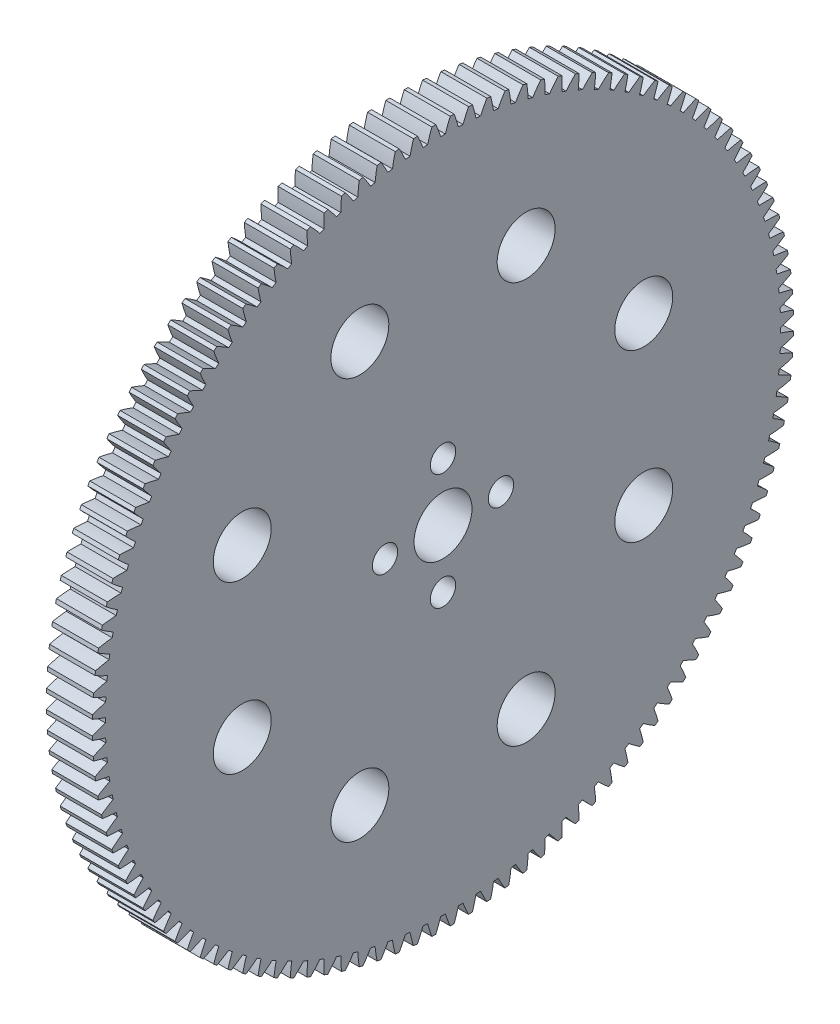
SolidWorks part; units mm, degrees
material "6061-T6 (SS)"
ref_plane "Plane1" through (0, 0, 0) normal (0, 0, 1) x (1, 0, 0)
ref_plane "Plane2" through (0, 0, 0) normal (0, 1, 0) x (1, 0, 0)
ref_plane "Plane3" through (0, 0, 0) normal (1, 0, 0) x (0, 0, -1)
sketch "HoldingSke" plane through (0, 0, 0) normal (0, 1, 0) x (1, 0, 0)
  line L0 (0, 0) -> (-406.4, -703.9054)
  line L1 (-15, 0) -> (100, 0) construction
  line L2 (0, 0) -> (-2.1039, 2.3779)
  line L3 (0, 0) -> (-11.863, 4.5341)
  line L4 (0, 0) -> (-4.318, 7.479)
  line L5 (0, 0) -> (-47.5972, -17.7524)
  line L6 (0, 0) -> (-5.2639, -3.5516)
  line L7 (-2.1039, 2.3779) -> (8.8308, 51.9871)
  line L8 (-76.2, 54.61) -> (-69.596, 54.61)
  line L9 (-71.009, 38.7566) -> (-53.1078, 45.2721)
  line L10 (-76.2, 71.12) -> (104.1128, 71.12)
  line L11 (0, 0) -> (-6.35, 0)
  line L12 (-76.2, 101.6) -> (-76.1716, 101.6)
  line L13 (24.9733, 27.94) -> (52.9518, 28.4284)
  line L14 (24.9733, 27.94) -> (25.0241, 27.9398)
  line L15 (24.9733, 27.94) -> (100.4021, 29.52)
  circle A0 centre (0, 0) radius 3.175
  circle A1 centre (0, 0) radius 38.1
  circle A2 centre (0, 0) radius 38.1
  circle A3 centre (0, 0) radius 3.175
  dimension "MHD" = 76.2
  dimension "Hub_dia" = 76.2
  dimension "Bore" = 6.35
  dimension "MBD" = 6.35
  dimension "Num_teeth" = 120
  dimension "Pitch" = 812.8
  dimension "Overall_len" = 50.8
  dimension "Show_teeth" = 120
  dimension "Thickness" = 6.35
  dimension "OAL" = 50.8001
  dimension "T_dim" = 6.604
  dimension "Ap" = 20
  dimension "H" = 19.05
  dimension "Pitch_radius" = 180.3128
  dimension "Width" = 6.35
  dimension "Backlash" = 0.0284
  dimension "Addendum_fac" = 1
  dimension "Dedendum_fac" = 1.2
  dimension "Clearance_fac" = 0.2
  dimension "Dedendum_add" = 0.0508
sketch "BasProSke" plane through (0, 0, 0) normal (0, 1, 0) x (1, 0, 0)
  line L0 (-10, 0) -> (60, 0) construction
  line L1 (0, 0) -> (0, 48.4187)
  line L2 (0, 0) -> (6.35, 0)
  line L3 (6.35, 0) -> (6.35, 48.4187)
  line L4 (6.35, 48.4187) -> (0, 48.4187)
  dimension "Thickness" = 6.35
  dimension "Diameter" = 96.8375
revolve "Base-Revolve" add sketch "BasProSke" angle 360 about L0
sketch "TooCutSke" plane through (0, 0, 0) normal (1, 0, 0) x (0, 0, -1)
  line L1 (0, 0) -> (0, 107) construction
  line L2 (0, 0) -> (-0.6732, 47.6202) construction
  line L3 (0, 0) -> (-2.4932, 95.2105) construction
  line L4 (-0.6732, 47.6202) -> (-1.2466, 47.6052) construction
  arc A0 (0.3197, 46.6206) -> (-0.3197, 46.6206) centre (0, 0) ccw
  arc A1 (1.0083, 48.4337) -> (-1.0083, 48.4337) centre (0, 0) ccw
  circle A2 centre (0, 0) radius 47.625 construction
  circle A3 centre (0, 0) radius 44.7529 construction
  arc A4 (-0.3197, 46.6206) -> (-1.0083, 48.4337) centre (-18.45, 40.7728) ccw
  arc A5 (1.0083, 48.4337) -> (0.3197, 46.6206) centre (18.45, 40.7728) ccw
  dimension "Root_dia" = 93.2434
  dimension "Overcut_dia" = 96.8883
  dimension "Pitch_dia" = 95.25
  dimension "Base_dia" = 89.5057
  dimension "Flank_rad" = 19.05
  dimension "Half_ang" = 1.5
  dimension "Half_CT" = 0.5736
extrude "ToothCut" cut sketch "TooCutSke" along normal through all
fillet "Breaks" [suppressed] radius 0.0159
fillet "RootFillets" [suppressed] radius 0.2095
pattern_circular "TeethCuts" count 120 every 3 about axis through (-10, 0, 0) along (1, 0, 0) of "ToothCut", "RootFillets", "Breaks"
sketch "HubNeaOneSke" plane through (0, 0, 0) normal (-1, 0, 0) x (0, 0, 1)
  circle A0 centre (0, 0) radius 38.1
  dimension "Diameter" = 76.2
extrude "HubNearOne" [suppressed] add sketch "HubNeaOneSke" along normal blind 44.4501
sketch "HubNeaBotSke" plane through (0, 0, 0) normal (-1, 0, 0) x (0, 0, 1)
  circle A0 centre (0, 0) radius 38.1
  dimension "Diameter" = 76.2
extrude "HubNearBoth" [suppressed] add sketch "HubNeaBotSke" along normal blind 22.225
ref_plane "FarPln" through (6.35, 0, 0) normal (1, 0, 0) x (0, 0, -1)
sketch "HubFarSke" plane through (6.35, 0, 0) normal (1, 0, 0) x (0, 0, -1)
  circle A0 centre (0, 0) radius 38.1
  dimension "Diameter" = 76.2
extrude "HubFar" [suppressed] add sketch "HubFarSke" along normal blind 22.225
sketch "BorSke" plane through (0, 0, 0) normal (1, 0, 0) x (0, 0, -1)
  circle A0 centre (0, 0) radius 3.175
  dimension "Diameter" = 6.35
extrude "Bore" cut sketch "BorSke" along normal mid plane 101.6001
sketch "KeySke" plane through (0, 0, 0) normal (1, 0, 0) x (0, 0, -1)
  line L0 (-0.127, 0) -> (-0.127, 3.429)
  line L1 (-0.127, 3.429) -> (0.127, 3.429)
  line L2 (0.127, 3.429) -> (0.127, 0)
  line L3 (0, 0) -> (0, 34) construction
  line L4 (-0.127, 0) -> (0.127, 0)
  dimension "Offset" = 3.429
  dimension "Width" = 0.254
extrude "Keyway" [suppressed] cut sketch "KeySke" along normal mid plane 101.6001
pattern_circular "Keyway2" [suppressed] count 2 every 90 about axis through (-10, 0, 0) along (1, 0, 0)
sketch "Sketch1" plane through (0, 0, 0) normal (1, 0, 0) x (0, 0, -1)
  line L0 (0, 0) -> (0, 52.1423) construction
  line L1 (0, 0) -> (11.4805, 27.7164) construction
  circle A5 centre (0, 8) radius 1.75
  circle A6 centre (-8, 0) radius 1.75
  circle A7 centre (0, 0) radius 4
  circle A8 centre (8, 0) radius 1.75
  circle A9 centre (0, -8) radius 1.75
  circle A10 centre (11.4805, 27.7164) radius 4 construction
  dimension "D1" = 8
  dimension "D3" = 30
  dimension "D2" = 22.5
extrude "Cut-Extrude2" cut sketch "Sketch1" along normal through all
sketch "Sketch3" plane through (0, 0, 0) normal (1, 0, 0) x (0, 0, -1)
  circle A0 centre (11.4805, 27.7164) radius 4 construction
  circle A1 centre (11.4805, 27.7164) radius 4
extrude "Cut-Extrude4" cut sketch "Sketch3" along normal through all
pattern_circular "CirPattern1" count 8 over 360 about axis through (0, 0, 0) along (1, 0, 0) of "Cut-Extrude4"
ref_plane "Plane4" through (3.1, 0, 0) normal (1, 0, 0) x (0, 0, -1)
sketch "Sketch4" plane through (3.1, 0, 0) normal (1, 0, 0) x (0, 0, -1)
  circle A0 centre (0, 0) radius 47.625 construction
  circle A1 centre (57.9795, 25.8965) radius 15.875 construction
  circle A2 centre (0, 0) radius 63.5 construction
  dimension "D1" = 95.25
  dimension "D2" = 31.75
equation "' \"Pitch@HoldingSke\" = 4"
equation "' \"Num_teeth@HoldingSke\" = 12"
equation "' \"Ap@HoldingSke\" =  20"
equation "' \"Ap@HoldingSke\" = 20"
equation "' \"Width@HoldingSke\" = 0.5"
equation "' \"Hub_dia@HoldingSke\"= 1"
equation "' \"Hub_dia@HoldingSke\" = 1"
equation "' \"Overall_len@HoldingSke\" = 1.0"
equation "' \"Bore@HoldingSke\" = 0.75"
equation "' \"T_dim@HoldingSke\" = 0.85"
equation "' \"Width@KeySke\" = 0.25"
equation "' \"Show_teeth@HoldingSke\" = 13"
equation "' \"Backlash@HoldingSke\" = 0.009"
equation "' \"Addendum_fac@HoldingSke\" = 1.0"
equation "' \"Dedendum_fac@HoldingSke\" = 1.25"
equation "' \"Dedendum_add@HoldingSke\" = 0.00005"
equation "' \"Clearance_fac@HoldingSke\" = 0.25"
equation "' \"Pitch@HoldingSke\" = 0.5"
equation "' \"Num_teeth@HoldingSke\" = 23"
equation "' \"Show_teeth@HoldingSke\" = 23"
equation "' \"Backlash@HoldingSke\" = 0.0375"
equation "\"Overcut_dia@TooCutSke\" = (\"Num_teeth@HoldingSke\" + 2 * \"Addendum_fac@HoldingSke\") / \"Pitch@HoldingSke\" + 0.002"
equation "\"Pitch_dia@TooCutSke\" = \"Num_teeth@HoldingSke\" / \"Pitch@HoldingSke\""
equation "\"Base_dia@TooCutSke\" = \"Num_teeth@HoldingSke\" / \"Pitch@HoldingSke\" * cos((\"Ap@HoldingSke\"  * 3.14159265 / 180))"
equation "\"Root_dia@TooCutSke\" = (\"Num_teeth@HoldingSke\" + 2) / \"Pitch@HoldingSke\" - 2 * (\"Addendum_fac@HoldingSke\" + \"Dedendum_fac@HoldingSke\") / \"Pitch@HoldingSke\" - \"Dedendum_add@HoldingSke\" * 2"
equation "\"Half_ang@TooCutSke\" = 180 / \"Num_teeth@HoldingSke\""
equation "\"Half_CT@TooCutSke\" = \"Num_teeth@HoldingSke\" / \"Pitch@HoldingSke\" * sin((3.14159265 / 2 / \"Num_teeth@HoldingSke\")) / 2 - 7 * \"Backlash@HoldingSke\" / 4"
equation "\"Flank_rad@TooCutSke\" = \"Num_teeth@HoldingSke\" / \"Pitch@HoldingSke\" / 5"
equation "\"Radius@RootFillets\" = \"Clearance_fac@HoldingSke\" / \"Pitch@HoldingSke\" + \"Dedendum_add@HoldingSke\""
equation "\"Break_rad@Breaks\" = 0.02 / \"Pitch@HoldingSke\""
equation "\"Thickness@HoldingSke\" = \"Width@HoldingSke\""
equation "\"OAL@HoldingSke\" = \"Thickness@HoldingSke\""
equation "\"MHD@HoldingSke\" = (\"Num_teeth@HoldingSke\" + 2) / \"Pitch@HoldingSke\" - 2 * (\"Addendum_fac@HoldingSke\" + \"Dedendum_fac@HoldingSke\")  / \"Pitch@HoldingSke\" - \"Dedendum_add@HoldingSke\" * 2"
equation "\"MBD@HoldingSke\" = (\"Num_teeth@HoldingSke\" + 2) / \"Pitch@HoldingSke\" - 2 * (\"Addendum_fac@HoldingSke\" + \"Dedendum_fac@HoldingSke\")  / \"Pitch@HoldingSke\" - \"Dedendum_add@HoldingSke\" * 2 - 0.002"
equation "\"MHD@HoldingSke\" = ((sgn( \"MHD@HoldingSke\" - \"Hub_dia@HoldingSke\" )-1)*( \"MHD@HoldingSke\" - \"Hub_dia@HoldingSke\" ))/-2+ \"Hub_dia@HoldingSke\""
equation "\"MBD@HoldingSke\" = ((sgn( \"MBD@HoldingSke\" - \"Bore@HoldingSke\" )-1)*( \"MBD@HoldingSke\" - \"Bore@HoldingSke\" ))/-2+ \"Bore@HoldingSke\""
equation "\"OAL@HoldingSke\" = ((sgn( \"OAL@HoldingSke\" - \"Overall_len@HoldingSke\" )+1)*( \"OAL@HoldingSke\" - \"Overall_len@HoldingSke\" ))/2 + \"Overall_len@HoldingSke\" + 0.000002"
equation "\"Num_teeth@TeethCuts\" = int( \"Show_teeth@HoldingSke\" ) + 1"
equation "\"Num_teeth@TeethCuts\" = ((sgn( \"Num_teeth@TeethCuts\" - \"Num_teeth@HoldingSke\" )-1)*( \"Num_teeth@TeethCuts\" - \"Num_teeth@HoldingSke\" ))/-2+ \"Num_teeth@HoldingSke\""
equation "\"Num_teeth@TeethCuts\" = ((sgn( \"Num_teeth@TeethCuts\" - 2.0)+1)*( \"Num_teeth@TeethCuts\" - 2.0))/2 +2.0"
equation "\"Angle@TeethCuts\" = 360.0 / \"Num_teeth@HoldingSke\""
equation "\"Diameter@BasProSke\" = (\"Num_teeth@HoldingSke\" + 2 * \"Addendum_fac@HoldingSke\") / \"Pitch@HoldingSke\""
equation "\"Thickness@BasProSke\"  = \"Thickness@HoldingSke\""
equation "' \"Fillet_rad@BasProSke\" =  \"Thickness@HoldingSke\" * 0.05"
equation "' \"Fillet_rad@BasProSke\" = \"Thickness@HoldingSke\" * 0.05"
equation "\"MHD@HoldingSke\" = ((sgn( \"MHD@HoldingSke\" - \"Root_dia@TooCutSke\" )-1)*( \"MHD@HoldingSke\" - \"Root_dia@TooCutSke\" ))/-2+ \"Root_dia@TooCutSke\""
equation "\"Diameter@HubNeaOneSke\" = \"MHD@HoldingSke\""
equation "\"Length@HubNearOne\" = \"OAL@HoldingSke\" - \"Thickness@BasProSke\""
equation "\"Diameter@HubNeaBotSke\" = \"MHD@HoldingSke\""
equation "\"Length@HubNearBoth\" = ( \"OAL@HoldingSke\" - \"Thickness@BasProSke\" ) / 2.0"
equation "\"Thickness@FarPln\" = \"Thickness@BasProSke\""
equation "\"Diameter@HubFarSke\" = \"MHD@HoldingSke\""
equation "\"Length@HubFar\" = ( \"OAL@HoldingSke\" - \"Thickness@BasProSke\" ) / 2.0"
equation "\"Diameter@BorSke\" = \"MBD@HoldingSke\""
equation "\"D1@Bore\" = \"OAL@HoldingSke\" * 2.0"
equation "\"D1@Keyway\" = \"OAL@HoldingSke\" * 2.0"
equation "\"Offset@KeySke\" = \"T_dim@HoldingSke\" - \"MBD@HoldingSke\" / 2.0"
